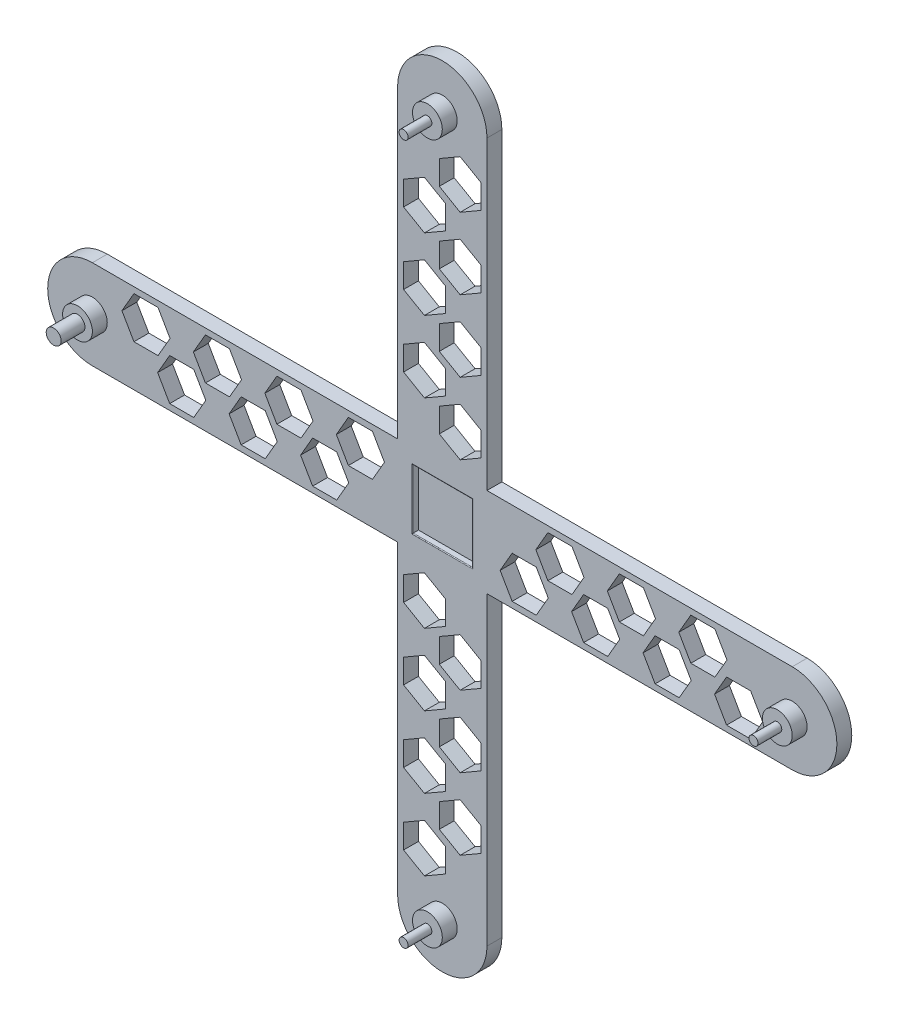
SolidWorks part; units mm, degrees
ref_plane "Front Plane" through (0, 0, 0) normal (0, 0, 1) x (1, 0, 0)
ref_plane "Top Plane" through (0, 0, 0) normal (0, 1, 0) x (1, 0, 0)
ref_plane "Right Plane" through (0, 0, 0) normal (1, 0, 0) x (0, 0, -1)
sketch "Sketch1" plane through (0, 0, 0) normal (0, 0, 1) x (1, 0, 0)
  line L0 (15, 15) -> (117.5, 15)
  line L1 (-15, 117.5) -> (15, 117.5) construction
  line L2 (-15, 117.5) -> (-15, 15)
  line L3 (-15, -117.5) -> (15, -117.5) construction
  line L4 (15, 117.5) -> (15, 15)
  line L5 (-15, 117.5) -> (15, -117.5) construction
  line L6 (-15, -117.5) -> (15, 117.5) construction
  line L7 (-117.5, 15) -> (-15, 15)
  line L8 (-117.5, 15) -> (-117.5, -15) construction
  line L9 (-117.5, -15) -> (-15, -15)
  line L10 (117.5, 15) -> (117.5, -15) construction
  line L11 (-117.5, 15) -> (117.5, -15) construction
  line L12 (-117.5, -15) -> (117.5, 15) construction
  line L13 (-15, -15) -> (-15, -117.5)
  line L14 (15, -15) -> (15, -117.5)
  line L15 (15, -15) -> (117.5, -15)
  line L16 (0, 132.5) -> (0, -132.5) construction
  line L17 (-132.5, 0) -> (132.5, 0) construction
  arc A0 (15, 117.5) -> (-15, 117.5) centre (0, 117.5) ccw
  arc A1 (-15, -117.5) -> (15, -117.5) centre (0, -117.5) ccw
  arc A2 (117.5, -15) -> (117.5, 15) centre (117.5, 0) ccw
  arc A3 (-117.5, 15) -> (-117.5, -15) centre (-117.5, 0) ccw
  point P0 (0, 0)
  point P6 (0, 0)
  point P16 (-117.5, 0)
  point P18 (0, -117.5)
  point P19 (117.5, 0)
  point P20 (0, 117.5)
  dimension "D1" = 235
  dimension "D2" = 30
  dimension "D3" = 30
  dimension "D4" = 235
  dimension "D5" = 117.5
extrude "Boss-Extrude1" add sketch "Sketch1" along normal blind 5
ref_plane "Plane1" through (0, 0, 5) normal (0, 0, 1) x (1, 0, 0)
sketch "Sketch5" plane through (0, 0, 5) normal (0, 0, 1) x (1, 0, 0)
  line L0 (-15, -117.5) -> (15, -117.5) construction
  circle A0 centre (-117.5, 0) radius 5
  circle A1 centre (0, -117.5) radius 5
  circle A2 centre (117.5, 0) radius 5
  circle A3 centre (0, 117.5) radius 5
  dimension "D1" = 10
  dimension "D2" = 10
  dimension "D3" = 10
  dimension "D4" = 10
extrude "Boss-Extrude2" add sketch "Sketch5" along normal blind 5
ref_plane "Plane2" through (0, 0, 10) normal (0, 0, 1) x (1, 0, 0)
sketch "Sketch7" plane through (0, 0, 10) normal (0, 0, 1) x (1, 0, 0)
  circle A0 centre (117.5, 0) radius 1.5
  circle A1 centre (0, -117.5) radius 1.5
  circle A2 centre (-117.5, 0) radius 2.5
  circle A3 centre (0, 117.5) radius 1.5
  dimension "D1" = 3
  dimension "D2" = 3
  dimension "D3" = 5
  dimension "D4" = 3
extrude "Boss-Extrude3" add sketch "Sketch7" along normal blind 8
sketch "Sketch8" plane through (0, 0, 5) normal (0, 0, 1) x (1, 0, 0)
  line L0 (6, 91.4171) -> (13, 95.4585)
  line L1 (-91.4171, 6) -> (-95.4585, 13)
  line L2 (-95.4585, 13) -> (-103.5415, 13)
  line L3 (-103.5415, 13) -> (-107.5829, 6)
  line L4 (-107.5829, 6) -> (-103.5415, -1)
  line L5 (-103.5415, -1) -> (-95.4585, -1)
  line L6 (-95.4585, -1) -> (-91.4171, 6)
  line L7 (-79.4171, -6) -> (-83.4585, 1)
  line L8 (-83.4585, 1) -> (-91.5415, 1)
  line L9 (-91.5415, 1) -> (-95.5829, -6)
  line L10 (-95.5829, -6) -> (-91.5415, -13)
  line L11 (-91.5415, -13) -> (-83.4585, -13)
  line L12 (-83.4585, -13) -> (-79.4171, -6)
  line L13 (-55.4171, -6) -> (-59.4585, 1)
  line L14 (-59.4585, 1) -> (-67.5415, 1)
  line L15 (-67.5415, 1) -> (-71.5829, -6)
  line L16 (-71.5829, -6) -> (-67.5415, -13)
  line L17 (-67.5415, -13) -> (-59.4585, -13)
  line L18 (-59.4585, -13) -> (-55.4171, -6)
  line L19 (-43.4171, 6) -> (-47.4585, 13)
  line L20 (-47.4585, 13) -> (-55.5415, 13)
  line L21 (-55.5415, 13) -> (-59.5829, 6)
  line L22 (-59.5829, 6) -> (-55.5415, -1)
  line L23 (-55.5415, -1) -> (-47.4585, -1)
  line L24 (-47.4585, -1) -> (-43.4171, 6)
  line L25 (-19.4171, 6) -> (-23.4585, 13)
  line L26 (-23.4585, 13) -> (-31.5415, 13)
  line L27 (-31.5415, 13) -> (-35.5829, 6)
  line L28 (-35.5829, 6) -> (-31.5415, -1)
  line L29 (-31.5415, -1) -> (-23.4585, -1)
  line L30 (-23.4585, -1) -> (-19.4171, 6)
  line L31 (-31.4171, -6) -> (-35.4585, 1)
  line L32 (-35.4585, 1) -> (-43.5415, 1)
  line L33 (-43.5415, 1) -> (-47.5829, -6)
  line L34 (-47.5829, -6) -> (-43.5415, -13)
  line L35 (-43.5415, -13) -> (-35.4585, -13)
  line L36 (-35.4585, -13) -> (-31.4171, -6)
  line L37 (13, 95.4585) -> (13, 103.5415)
  line L44 (-67.4171, 6) -> (-71.4585, 13)
  line L45 (-71.4585, 13) -> (-79.5415, 13)
  line L46 (-79.5415, 13) -> (-83.5829, 6)
  line L47 (-83.5829, 6) -> (-79.5415, -1)
  line L48 (-79.5415, -1) -> (-71.4585, -1)
  line L49 (-71.4585, -1) -> (-67.4171, 6)
  line L50 (13, 103.5415) -> (6, 107.5829)
  line L51 (6, 107.5829) -> (-1, 103.5415)
  line L52 (-1, 103.5415) -> (-1, 95.4585)
  line L53 (-1, 95.4585) -> (6, 91.4171)
  line L54 (-6, 79.4171) -> (1, 83.4585)
  line L55 (1, 83.4585) -> (1, 91.5415)
  line L56 (1, 91.5415) -> (-6, 95.5829)
  line L57 (-6, 95.5829) -> (-13, 91.5415)
  line L58 (-13, 91.5415) -> (-13, 83.4585)
  line L59 (-13, 83.4585) -> (-6, 79.4171)
  line L60 (6, 67.4171) -> (13, 71.4585)
  line L61 (13, 71.4585) -> (13, 79.5415)
  line L62 (13, 79.5415) -> (6, 83.5829)
  line L63 (6, 83.5829) -> (-1, 79.5415)
  line L64 (-1, 79.5415) -> (-1, 71.4585)
  line L65 (-1, 71.4585) -> (6, 67.4171)
  line L66 (-6, 55.4171) -> (1, 59.4585)
  line L67 (1, 59.4585) -> (1, 67.5415)
  line L68 (1, 67.5415) -> (-6, 71.5829)
  line L69 (-6, 71.5829) -> (-13, 67.5415)
  line L70 (-13, 67.5415) -> (-13, 59.4585)
  line L71 (-13, 59.4585) -> (-6, 55.4171)
  line L72 (6, 43.4171) -> (13, 47.4585)
  line L73 (13, 47.4585) -> (13, 55.5415)
  line L74 (13, 55.5415) -> (6, 59.5829)
  line L75 (6, 59.5829) -> (-1, 55.5415)
  line L76 (-1, 55.5415) -> (-1, 47.4585)
  line L77 (-1, 47.4585) -> (6, 43.4171)
  line L78 (-6, 31.4171) -> (1, 35.4585)
  line L79 (1, 35.4585) -> (1, 43.5415)
  line L80 (1, 43.5415) -> (-6, 47.5829)
  line L81 (-6, 47.5829) -> (-13, 43.5415)
  line L82 (-13, 43.5415) -> (-13, 35.4585)
  line L83 (-13, 35.4585) -> (-6, 31.4171)
  line L84 (6, 19.4171) -> (13, 23.4585)
  line L85 (13, 23.4585) -> (13, 31.5415)
  line L86 (13, 31.5415) -> (6, 35.5829)
  line L87 (6, 35.5829) -> (-1, 31.5415)
  line L88 (-1, 31.5415) -> (-1, 23.4585)
  line L89 (-1, 23.4585) -> (6, 19.4171)
  line L90 (91.4171, -6) -> (95.4585, -13)
  line L91 (95.4585, -13) -> (103.5415, -13)
  line L92 (103.5415, -13) -> (107.5829, -6)
  line L93 (107.5829, -6) -> (103.5415, 1)
  line L94 (103.5415, 1) -> (95.4585, 1)
  line L95 (95.4585, 1) -> (91.4171, -6)
  line L96 (79.4171, 6) -> (83.4585, -1)
  line L97 (83.4585, -1) -> (91.5415, -1)
  line L98 (91.5415, -1) -> (95.5829, 6)
  line L99 (95.5829, 6) -> (91.5415, 13)
  line L100 (91.5415, 13) -> (83.4585, 13)
  line L101 (83.4585, 13) -> (79.4171, 6)
  line L102 (67.4171, -6) -> (71.4585, -13)
  line L103 (71.4585, -13) -> (79.5415, -13)
  line L104 (79.5415, -13) -> (83.5829, -6)
  line L105 (83.5829, -6) -> (79.5415, 1)
  line L106 (79.5415, 1) -> (71.4585, 1)
  line L107 (71.4585, 1) -> (67.4171, -6)
  line L108 (55.4171, 6) -> (59.4585, -1)
  line L109 (59.4585, -1) -> (67.5415, -1)
  line L110 (67.5415, -1) -> (71.5829, 6)
  line L111 (71.5829, 6) -> (67.5415, 13)
  line L112 (67.5415, 13) -> (59.4585, 13)
  line L113 (59.4585, 13) -> (55.4171, 6)
  line L114 (43.4171, -6) -> (47.4585, -13)
  line L115 (47.4585, -13) -> (55.5415, -13)
  line L116 (55.5415, -13) -> (59.5829, -6)
  line L117 (59.5829, -6) -> (55.5415, 1)
  line L118 (55.5415, 1) -> (47.4585, 1)
  line L119 (47.4585, 1) -> (43.4171, -6)
  line L120 (31.4171, 6) -> (35.4585, -1)
  line L121 (35.4585, -1) -> (43.5415, -1)
  line L122 (43.5415, -1) -> (47.5829, 6)
  line L123 (47.5829, 6) -> (43.5415, 13)
  line L124 (43.5415, 13) -> (35.4585, 13)
  line L125 (35.4585, 13) -> (31.4171, 6)
  line L126 (19.4171, -6) -> (23.4585, -13)
  line L127 (23.4585, -13) -> (31.5415, -13)
  line L128 (31.5415, -13) -> (35.5829, -6)
  line L129 (35.5829, -6) -> (31.5415, 1)
  line L130 (31.5415, 1) -> (23.4585, 1)
  line L131 (23.4585, 1) -> (19.4171, -6)
  line L132 (-6, -91.4171) -> (-13, -95.4585)
  line L133 (-13, -95.4585) -> (-13, -103.5415)
  line L134 (-13, -103.5415) -> (-6, -107.5829)
  line L135 (-6, -107.5829) -> (1, -103.5415)
  line L136 (1, -103.5415) -> (1, -95.4585)
  line L137 (1, -95.4585) -> (-6, -91.4171)
  line L138 (6, -79.4171) -> (-1, -83.4585)
  line L139 (-1, -83.4585) -> (-1, -91.5415)
  line L140 (-1, -91.5415) -> (6, -95.5829)
  line L141 (6, -95.5829) -> (13, -91.5415)
  line L142 (13, -91.5415) -> (13, -83.4585)
  line L143 (13, -83.4585) -> (6, -79.4171)
  line L144 (-6, -67.4171) -> (-13, -71.4585)
  line L145 (-13, -71.4585) -> (-13, -79.5415)
  line L146 (-13, -79.5415) -> (-6, -83.5829)
  line L147 (-6, -83.5829) -> (1, -79.5415)
  line L148 (1, -79.5415) -> (1, -71.4585)
  line L149 (1, -71.4585) -> (-6, -67.4171)
  line L150 (6, -55.4171) -> (-1, -59.4585)
  line L151 (-1, -59.4585) -> (-1, -67.5415)
  line L152 (-1, -67.5415) -> (6, -71.5829)
  line L153 (6, -71.5829) -> (13, -67.5415)
  line L154 (13, -67.5415) -> (13, -59.4585)
  line L155 (13, -59.4585) -> (6, -55.4171)
  line L156 (-6, -43.4171) -> (-13, -47.4585)
  line L157 (-13, -47.4585) -> (-13, -55.5415)
  line L158 (-13, -55.5415) -> (-6, -59.5829)
  line L159 (-6, -59.5829) -> (1, -55.5415)
  line L160 (1, -55.5415) -> (1, -47.4585)
  line L161 (1, -47.4585) -> (-6, -43.4171)
  line L162 (6, -31.4171) -> (-1, -35.4585)
  line L163 (-1, -35.4585) -> (-1, -43.5415)
  line L164 (-1, -43.5415) -> (6, -47.5829)
  line L165 (6, -47.5829) -> (13, -43.5415)
  line L166 (13, -43.5415) -> (13, -35.4585)
  line L167 (13, -35.4585) -> (6, -31.4171)
  line L168 (-6, -19.4171) -> (-13, -23.4585)
  line L169 (-13, -23.4585) -> (-13, -31.5415)
  line L170 (-13, -31.5415) -> (-6, -35.5829)
  line L171 (-6, -35.5829) -> (1, -31.5415)
  line L172 (1, -31.5415) -> (1, -23.4585)
  line L173 (1, -23.4585) -> (-6, -19.4171)
  circle A0 centre (-99.5, 6) radius 7 construction
  circle A1 centre (-87.5, -6) radius 7 construction
  circle A2 centre (-63.5, -6) radius 7 construction
  circle A3 centre (-51.5, 6) radius 7 construction
  circle A4 centre (-27.5, 6) radius 7 construction
  circle A5 centre (-39.5, -6) radius 7 construction
  circle A7 centre (-75.5, 6) radius 7 construction
  dimension "D1" = 14
  dimension "D5" = 14
  dimension "D7" = 14
  dimension "D10" = 14
  dimension "D11" = 14
  dimension "D14" = 14
  dimension "D16" = 14
  dimension "D2" = 6
  dimension "D3" = 18
  dimension "D4" = 6
  dimension "D6" = 12
  dimension "D8" = 12
  dimension "D9" = 12
  dimension "D12" = 12
  dimension "D13" = 12
  dimension "D15" = 12
  dimension "D17" = 4
extrude "Cut-Extrude1" cut sketch "Sketch8" against normal blind 8
sketch "Sketch11" plane through (0, 0, 5) normal (0, 0, 1) x (1, 0, 0)
  line L1 (-10, 10) -> (10, 10)
  line L2 (-10, 10) -> (-10, -10)
  line L3 (-10, -10) -> (10, -10)
  line L4 (10, 10) -> (10, -10)
  line L5 (-10, 10) -> (10, -10) construction
  line L6 (-10, -10) -> (10, 10) construction
  point P0 (0, 0)
  dimension "D1" = 20
  dimension "D2" = 20
extrude "Cut-Extrude3" cut sketch "Sketch11" against normal blind 2
fillet "Fillet8" radius 0.25 4 edges at (10, 0, 5) (0, 10, 5) (-10, 0, 5) (0, -10, 5)
